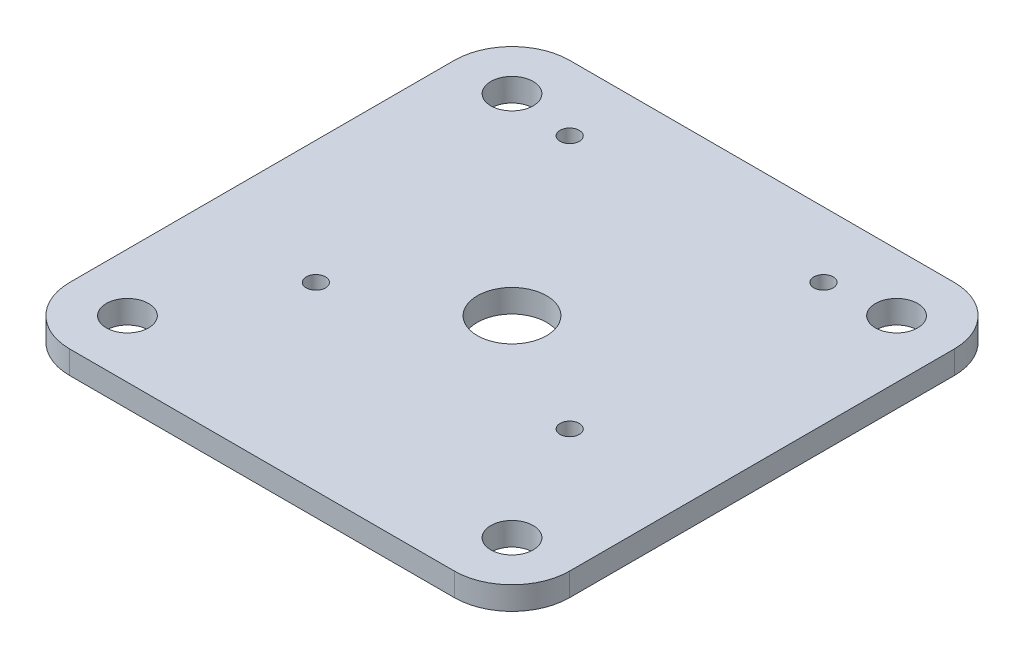
SolidWorks part; units mm, degrees
ref_plane "Front Plane" through (0, 0, 0) normal (0, 0, 1) x (1, 0, 0)
ref_plane "Top Plane" through (0, 0, 0) normal (0, 1, 0) x (1, 0, 0)
ref_plane "Right Plane" through (0, 0, 0) normal (1, 0, 0) x (0, 0, -1)
sketch "Sketch1" plane through (0, 0, 0) normal (0, 1, 0) x (1, 0, 0)
  line L1 (-50, -65) -> (50, -65)
  line L2 (-65, -50) -> (-65, 50)
  line L3 (-50, 65) -> (50, 65)
  line L4 (65, -50) -> (65, 50)
  line L5 (-65, -65) -> (65, 65) construction
  line L6 (-65, 65) -> (65, -65) construction
  arc A0 (-50, -65) -> (-65, -50) centre (-50, -50) cw
  arc A1 (-65, 50) -> (-50, 65) centre (-50, 50) cw
  arc A2 (65, 50) -> (50, 65) centre (50, 50) ccw
  arc A3 (50, -65) -> (65, -50) centre (50, -50) ccw
  circle A4 centre (0, 0) radius 9
  point P0 (0, 0)
  dimension "D1" = 15
  dimension "D2" = 18
  dimension "D3" = 130
extrude "Boss-Extrude1" add sketch "Sketch1" along normal blind 6
sketch "Sketch3" plane through (0, 6, 0) normal (0, 1, 0) x (1, 0, 0)
  line L1 (-50, -50) -> (50, -50) construction
  line L2 (-50, -50) -> (-50, 50) construction
  line L3 (-50, 50) -> (50, 50) construction
  line L4 (50, -50) -> (50, 50) construction
  line L5 (-50, -50) -> (50, 50) construction
  line L6 (-50, 50) -> (50, -50) construction
  circle A0 centre (-50, 50) radius 5.5
  circle A1 centre (50, 50) radius 5.5
  circle A2 centre (50, -50) radius 5.5
  circle A3 centre (-50, -50) radius 5.5
  point P0 (0, 0)
  dimension "D2" = 11
  dimension "D1" = 100
extrude "Cut-Extrude2" cut sketch "Sketch3" against normal through all both and the other way through all
sketch "Sketch6" plane through (0, 6, 0) normal (0, 1, 0) x (1, 0, 0)
  line L0 (100.0308, -49.0856) -> (98.931, 16.9052)
  line L1 (98.931, 16.9052) -> (164.9219, 18.005)
  line L2 (164.9219, 18.005) -> (166.0216, -47.9859)
  line L3 (166.0216, -47.9859) -> (132.7262, -47.9859)
  line L4 (132.7262, -47.9859) -> (132.7262, -30.5382)
  line L5 (-33, 48) -> (-33, -18) construction
  line L6 (-33, -18) -> (33, -18) construction
  line L7 (33, -18) -> (33, 48) construction
  line L8 (33, 48) -> (-33, 48) construction
  line L9 (0, 0) -> (0, 15) construction
  line L10 (33, 15) -> (-33, 15) construction
  circle A0 centre (166.0216, -47.9859) radius 2
  circle A1 centre (100.0308, -49.0856) radius 2
  circle A2 centre (164.9219, 18.005) radius 2
  circle A3 centre (98.931, 16.9052) radius 2
  circle A4 centre (132.7262, -30.5382) radius 33
  circle A5 centre (33, -18) radius 2.5
  circle A6 centre (33, 48) radius 2.5
  circle A7 centre (-33, 48) radius 2.5
  circle A8 centre (-33, -18) radius 2.5
  dimension "D3" = 5
  dimension "D1" = 66
  dimension "D2" = 15
extrude "Cut-Extrude3" cut sketch "Sketch6" against normal up to next contours A6 | A5 | A7 | A8
